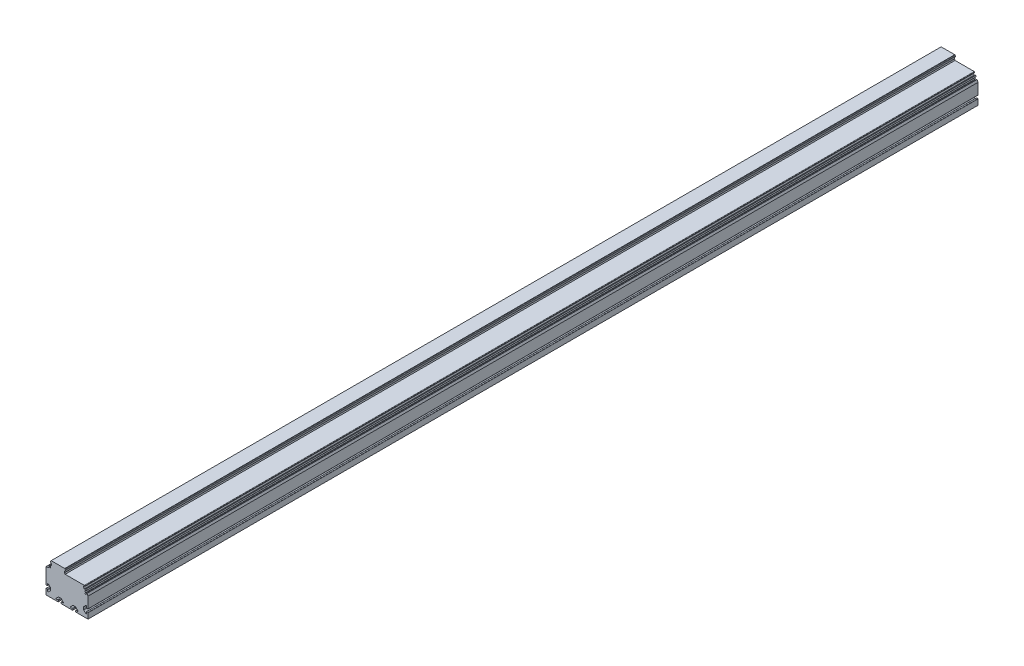
SolidWorks part; units mm, degrees
material "6061 Alloy"
ref_plane "Front Plane" through (0, 0, 0) normal (0, 0, 1) x (1, 0, 0)
ref_plane "Top Plane" through (0, 0, 0) normal (0, 1, 0) x (1, 0, 0)
ref_plane "Right Plane" through (0, 0, 0) normal (1, 0, 0) x (0, 0, -1)
ref_plane "Plane1" through (0, 0, 0) normal (0, 0, 1) x (1, 0, 0)
sketch "Sketch1" plane through (0, 0, 0) normal (0, 0, 1) x (1, 0, 0)
  line L0 (0, 0) -> (116, 0)
  line L1 (116, 0) -> (116, 55)
  line L2 (116, 55) -> (106.3474, 75.7)
  line L3 (106.3474, 75.7) -> (54, 75.7)
  line L4 (54, 75.7) -> (54, 89)
  line L5 (54, 89) -> (12, 89)
  line L6 (12, 89) -> (12, 75.9)
  line L7 (12, 75.9) -> (9.963, 75.9)
  line L8 (9.963, 75.9) -> (8, 72.5)
  line L9 (8, 72.5) -> (8, 68.3)
  line L10 (8, 68.3) -> (0, 68.3)
  line L11 (0, 68.3) -> (0, 0)
extrude "Boss-Extrude1" add sketch "Sketch1" against normal blind 2456
ref_plane "Plane2" through (0, 0, 0) normal (0, 0, 1) x (1, 0, 0)
sketch "Sketch2" plane through (0, 0, 0) normal (0, 0, 1) x (1, 0, 0)
  line L0 (-5, -5) -> (120, -5)
  line L1 (120, -5) -> (120, 95)
  line L2 (120, 95) -> (-5, 95)
  line L3 (-5, 95) -> (-5, -5)
  line L4 (0, 0) -> (33.3, 0)
  line L5 (34, 0.7) -> (34, 3.8)
  line L6 (33.3, 4.5) -> (31.3064, 4.5)
  line L7 (28.5126, 6.5374) -> (33.5464, 11.5713)
  line L8 (35.6678, 12.45) -> (40.3322, 12.45)
  line L9 (42.4536, 11.5713) -> (47.4874, 6.5374)
  line L10 (44.6936, 4.5) -> (42.7, 4.5)
  line L11 (42, 3.8) -> (42, 0.7)
  line L12 (42.7, 0) -> (73.3, 0)
  line L13 (74, 0.7) -> (74, 3.8)
  line L14 (73.3, 4.5) -> (71.3064, 4.5)
  line L15 (68.5126, 6.5374) -> (73.5464, 11.5713)
  line L16 (75.6678, 12.45) -> (80.3322, 12.45)
  line L17 (82.4536, 11.5713) -> (87.4874, 6.5374)
  line L18 (84.6936, 4.5) -> (82.7, 4.5)
  line L19 (82, 3.8) -> (82, 0.7)
  line L20 (82.7, 0) -> (116, 0)
  line L21 (116, 0) -> (116, 15.3)
  line L22 (115.3, 16) -> (112.2, 16)
  line L23 (111.5, 15.3) -> (111.5, 13.3064)
  line L24 (109.4626, 10.5126) -> (104.4287, 15.5464)
  line L25 (103.55, 17.6678) -> (103.55, 22.3322)
  line L26 (104.4287, 24.4536) -> (109.4626, 29.4874)
  line L27 (111.5, 26.6936) -> (111.5, 24.7)
  line L28 (112.2, 24) -> (115.3, 24)
  line L29 (116, 24.7) -> (116, 55)
  line L30 (116, 55) -> (113.4643, 60.4378)
  line L31 (112.9327, 60.6313) -> (112.2983, 60.3355)
  line L32 (112.2016, 60.0697) -> (112.6047, 59.2052)
  line L33 (112.5051, 58.6403) -> (110.0535, 56.1887)
  line L34 (107.9322, 58.3101) -> (108.8717, 59.2496)
  line L35 (108.9215, 59.532) -> (106.9136, 63.838)
  line L36 (107.1071, 64.3695) -> (109.4635, 65.4683)
  line L37 (109.7292, 65.3716) -> (109.8349, 65.145)
  line L38 (110.1007, 65.0483) -> (110.7351, 65.3441)
  line L39 (110.9286, 65.8757) -> (109.6607, 68.5946)
  line L40 (109.1292, 68.7881) -> (108.4947, 68.4923)
  line L41 (108.398, 68.2265) -> (108.5037, 67.9999)
  line L42 (108.4069, 67.7341) -> (106.0505, 66.6353)
  line L43 (105.5189, 66.8288) -> (103.11, 71.9947)
  line L44 (103.3035, 72.5263) -> (105.6599, 73.6251)
  line L45 (105.9257, 73.5284) -> (106.0313, 73.3018)
  line L46 (106.2971, 73.2051) -> (106.9315, 73.5009)
  line L47 (107.125, 74.0325) -> (106.6167, 75.1226)
  line L48 (105.7104, 75.7) -> (52.7702, 75.7)
  line L49 (52.7702, 75.7) -> (51.1, 78.5929)
  line L50 (51.1, 78.5929) -> (51.1, 81.84)
  line L51 (51.1, 81.84) -> (52.6709, 83.4109)
  line L52 (53.8041, 84.5441) -> (54, 84.74)
  line L53 (54, 84.74) -> (54, 86.75)
  line L54 (54, 86.75) -> (53.8041, 86.9459)
  line L55 (52.6709, 88.0791) -> (51.75, 89)
  line L56 (51.75, 89) -> (14.25, 89)
  line L57 (14.25, 89) -> (13.3291, 88.0791)
  line L58 (12.1959, 86.9459) -> (12, 86.75)
  line L59 (12, 86.75) -> (12, 84.74)
  line L60 (12, 84.74) -> (12.1959, 84.5441)
  line L61 (13.3291, 83.4109) -> (14.9, 81.84)
  line L62 (14.9, 81.84) -> (14.9, 78.5929)
  line L63 (14.9, 78.5929) -> (12, 73.57)
  line L64 (12, 73.57) -> (12, 72.5)
  line L65 (12, 72.5) -> (13.45, 72.5)
  line L66 (13.45, 72.5) -> (13.45, 72.4)
  line L67 (13.45, 72.4) -> (13.25, 72.4)
  line L68 (12.75, 71.9) -> (12.75, 70.9)
  line L69 (12.25, 70.4) -> (12.05, 70.4)
  line L70 (11.55, 70.9) -> (11.55, 71.4439)
  line L71 (11.008, 72.5) -> (11.5454, 75.5479)
  line L72 (11.25, 75.9) -> (10.2517, 75.9)
  line L73 (9.8187, 75.65) -> (8.134, 72.7321)
  line L74 (8, 72.2321) -> (8, 68.3)
  line L75 (8, 68.3) -> (1.2, 68.3)
  line L76 (0, 67.1) -> (0, 24.7)
  line L77 (0.7, 24) -> (3.8, 24)
  line L78 (4.5, 24.7) -> (4.5, 26.6936)
  line L79 (6.5374, 29.4874) -> (11.5713, 24.4536)
  line L80 (12.45, 22.3322) -> (12.45, 17.6678)
  line L81 (11.5713, 15.5464) -> (6.5374, 10.5126)
  line L82 (4.5, 13.3064) -> (4.5, 15.3)
  line L83 (3.8, 16) -> (0.7, 16)
  line L84 (0, 15.3) -> (0, 0)
  arc A0 (33.3, 0) -> (34, 0.7) centre (33.3, 0.7) ccw
  arc A1 (34, 3.8) -> (33.3, 4.5) centre (33.3, 3.8) ccw
  arc A2 (31.3064, 4.5) -> (28.5126, 6.5374) centre (29.75, 5.3) cw
  arc A3 (33.5464, 11.5713) -> (35.6678, 12.45) centre (35.6678, 9.45) cw
  arc A4 (40.3322, 12.45) -> (42.4536, 11.5713) centre (40.3322, 9.45) cw
  arc A5 (47.4874, 6.5374) -> (44.6936, 4.5) centre (46.25, 5.3) cw
  arc A6 (42.7, 4.5) -> (42, 3.8) centre (42.7, 3.8) ccw
  arc A7 (42, 0.7) -> (42.7, 0) centre (42.7, 0.7) ccw
  arc A8 (73.3, 0) -> (74, 0.7) centre (73.3, 0.7) ccw
  arc A9 (74, 3.8) -> (73.3, 4.5) centre (73.3, 3.8) ccw
  arc A10 (71.3064, 4.5) -> (68.5126, 6.5374) centre (69.75, 5.3) cw
  arc A11 (73.5464, 11.5713) -> (75.6678, 12.45) centre (75.6678, 9.45) cw
  arc A12 (80.3322, 12.45) -> (82.4536, 11.5713) centre (80.3322, 9.45) cw
  arc A13 (87.4874, 6.5374) -> (84.6936, 4.5) centre (86.25, 5.3) cw
  arc A14 (82.7, 4.5) -> (82, 3.8) centre (82.7, 3.8) ccw
  arc A15 (82, 0.7) -> (82.7, 0) centre (82.7, 0.7) ccw
  arc A16 (116, 15.3) -> (115.3, 16) centre (115.3, 15.3) ccw
  arc A17 (112.2, 16) -> (111.5, 15.3) centre (112.2, 15.3) ccw
  arc A18 (111.5, 13.3064) -> (109.4626, 10.5126) centre (110.7, 11.75) cw
  arc A19 (104.4287, 15.5464) -> (103.55, 17.6678) centre (106.55, 17.6678) cw
  arc A20 (103.55, 22.3322) -> (104.4287, 24.4536) centre (106.55, 22.3322) cw
  arc A21 (109.4626, 29.4874) -> (111.5, 26.6936) centre (110.7, 28.25) cw
  arc A22 (111.5, 24.7) -> (112.2, 24) centre (112.2, 24.7) ccw
  arc A23 (115.3, 24) -> (116, 24.7) centre (115.3, 24.7) ccw
  arc A24 (113.4643, 60.4378) -> (112.9327, 60.6313) centre (113.1018, 60.2688) ccw
  arc A25 (112.2983, 60.3355) -> (112.2016, 60.0697) centre (112.3828, 60.1542) ccw
  arc A26 (112.6047, 59.2052) -> (112.5051, 58.6403) centre (112.1515, 58.9939) cw
  arc A27 (110.0535, 56.1887) -> (107.9322, 58.3101) centre (108.9928, 57.2494) cw
  arc A28 (108.8717, 59.2496) -> (108.9215, 59.532) centre (108.6949, 59.4263) ccw
  arc A29 (106.9136, 63.838) -> (107.1071, 64.3695) centre (107.2761, 64.007) cw
  arc A30 (109.4635, 65.4683) -> (109.7292, 65.3716) centre (109.548, 65.2871) cw
  arc A31 (109.8349, 65.145) -> (110.1007, 65.0483) centre (110.0162, 65.2296) ccw
  arc A32 (110.7351, 65.3441) -> (110.9286, 65.8757) centre (110.5661, 65.7066) ccw
  arc A33 (109.6607, 68.5946) -> (109.1292, 68.7881) centre (109.2982, 68.4256) ccw
  arc A34 (108.4947, 68.4923) -> (108.398, 68.2265) centre (108.5793, 68.311) ccw
  arc A35 (108.5037, 67.9999) -> (108.4069, 67.7341) centre (108.3224, 67.9154) cw
  arc A36 (106.0505, 66.6353) -> (105.5189, 66.8288) centre (105.8815, 66.9978) cw
  arc A37 (103.11, 71.9947) -> (103.3035, 72.5263) centre (103.4725, 72.1638) cw
  arc A38 (105.6599, 73.6251) -> (105.9257, 73.5284) centre (105.7444, 73.4439) cw
  arc A39 (106.0313, 73.3018) -> (106.2971, 73.2051) centre (106.2126, 73.3863) ccw
  arc A40 (106.9315, 73.5009) -> (107.125, 74.0325) centre (106.7625, 73.8634) ccw
  arc A41 (106.6167, 75.1226) -> (105.7104, 75.7) centre (105.7104, 74.7) ccw
  arc A42 (52.6709, 83.4109) -> (53.8041, 84.5441) centre (54.075, 83.14) cw
  arc A43 (53.8041, 86.9459) -> (52.6709, 88.0791) centre (54.075, 88.35) cw
  arc A44 (13.3291, 88.0791) -> (12.1959, 86.9459) centre (11.925, 88.35) cw
  arc A45 (12.1959, 84.5441) -> (13.3291, 83.4109) centre (11.925, 83.14) cw
  arc A46 (13.25, 72.4) -> (12.75, 71.9) centre (13.25, 71.9) ccw
  arc A47 (12.75, 70.9) -> (12.25, 70.4) centre (12.25, 70.9) cw
  arc A48 (12.05, 70.4) -> (11.55, 70.9) centre (12.05, 70.9) cw
  arc A49 (11.55, 71.4439) -> (11.3415, 71.8501) centre (11.05, 71.4439) ccw
  arc A50 (11.3415, 71.8501) -> (11.008, 72.5) centre (11.808, 72.5) cw
  arc A51 (11.5454, 75.5479) -> (11.25, 75.9) centre (11.25, 75.6) ccw
  arc A52 (10.2517, 75.9) -> (9.8187, 75.65) centre (10.2517, 75.4) ccw
  arc A53 (8.134, 72.7321) -> (8, 72.2321) centre (9, 72.2321) ccw
  arc A54 (1.2, 68.3) -> (0, 67.1) centre (1.2, 67.1) ccw
  arc A55 (0, 24.7) -> (0.7, 24) centre (0.7, 24.7) ccw
  arc A56 (3.8, 24) -> (4.5, 24.7) centre (3.8, 24.7) ccw
  arc A57 (4.5, 26.6936) -> (6.5374, 29.4874) centre (5.3, 28.25) cw
  arc A58 (11.5713, 24.4536) -> (12.45, 22.3322) centre (9.45, 22.3322) cw
  arc A59 (12.45, 17.6678) -> (11.5713, 15.5464) centre (9.45, 17.6678) cw
  arc A60 (6.5374, 10.5126) -> (4.5, 13.3064) centre (5.3, 11.75) cw
  arc A61 (4.5, 15.3) -> (3.8, 16) centre (3.8, 15.3) ccw
  arc A62 (0.7, 16) -> (0, 15.3) centre (0.7, 15.3) ccw
extrude "Cut-Extrude1" cut sketch "Sketch2" against normal blind 2456
ref_plane "Plane3" through (0, 0, 0) normal (0, 0, 1) x (1, 0, 0)
sketch "Sketch3" plane through (0, 0, 0) normal (0, 0, 1) x (1, 0, 0)
  line L0 (6, 67.3) -> (9, 67.3)
  line L1 (9, 67.3) -> (9, 70.3)
  line L2 (9, 70.3) -> (8, 70.3)
  line L3 (6, 68.3) -> (6, 67.3)
  arc A0 (8, 70.3) -> (6, 68.3) centre (6, 70.3) cw
extrude "Boss-Extrude2" add sketch "Sketch3" against normal blind 2456
ref_plane "Plane4" through (0, 0, -2454) normal (0, 0, 1) x (1, 0, 0)
sketch "Sketch4" plane through (0, 0, -2454) normal (0, 0, 1) x (1, 0, 0)
  line L0 (64.3249, 20.2806) -> (85.2885, 19.1819)
  arc A0 (85.2885, 19.1819) -> (64.3249, 20.2806) centre (76, 42.5) ccw
extrude "Cut-Extrude2" cut sketch "Sketch4" against normal blind 2
